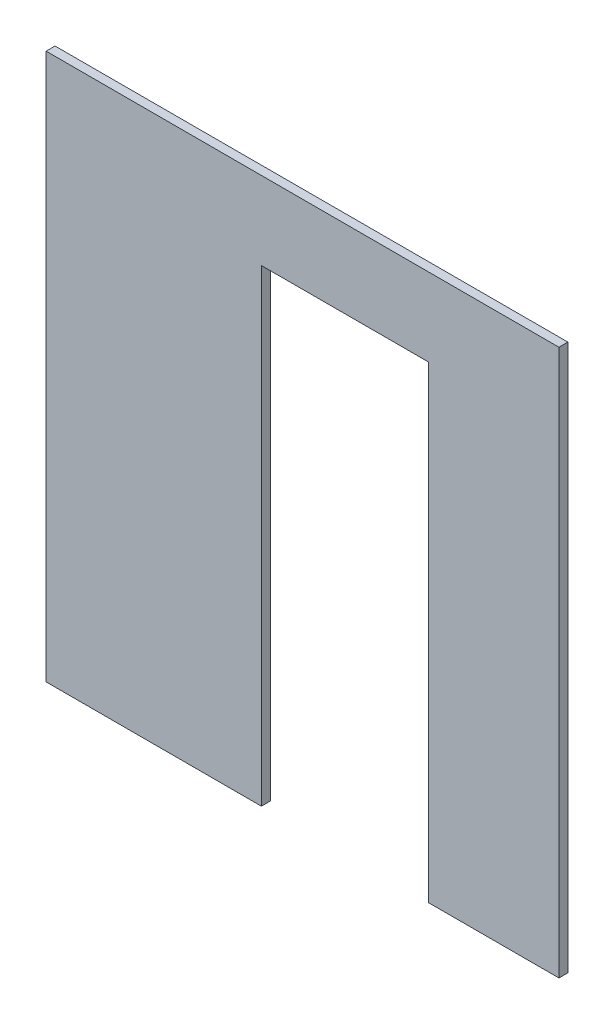
SolidWorks part; units mm, degrees
ref_plane "Front Plane" through (0, 0, 0) normal (0, 0, 1) x (1, 0, 0)
ref_plane "Top Plane" through (0, 0, 0) normal (0, 1, 0) x (1, 0, 0)
ref_plane "Right Plane" through (0, 0, 0) normal (1, 0, 0) x (0, 0, -1)
sketch "Sketch1" plane through (0, 0, 0) normal (0, 0, 1) x (1, 0, 0)
  line L1 (0, 0) -> (2300, 0)
  line L2 (0, 0) -> (0, 2450)
  line L3 (0, 2450) -> (2300, 2450)
  line L4 (2300, 0) -> (2300, 2450)
extrude "Boss-Extrude1" add sketch "Sketch1" along normal blind 40
sketch "Sketch2" plane through (0, 0, 0) normal (0, 0, 1) x (1, 0, 0)
  line L1 (0, 0) -> (2300, 0) construction
  line L3 (1715.402, 0) -> (965.402, 0)
  line L4 (1715.402, 0) -> (1715.402, 2100)
  line L5 (1715.402, 2100) -> (965.402, 2100)
  line L6 (965.402, 0) -> (965.402, 2100)
extrude "Cut-Extrude1" cut sketch "Sketch2" against normal blind 100 and the other way blind 100
